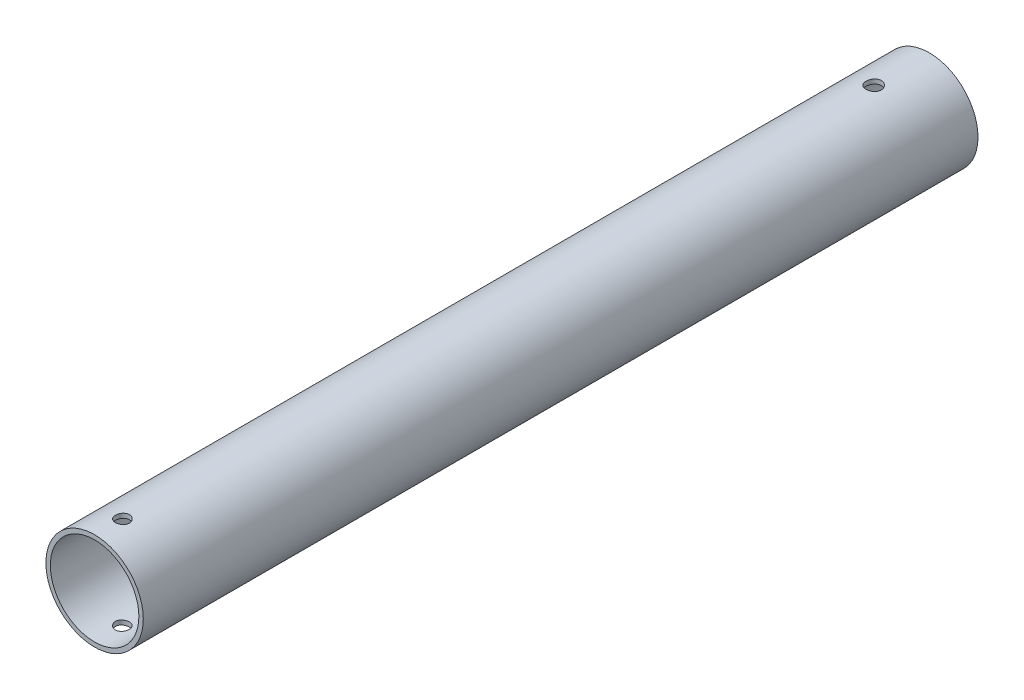
SolidWorks part; units mm, degrees
material "1060 Alloy"
ref_plane "Front Plane" through (0, 0, 0) normal (0, 0, 1) x (1, 0, 0)
ref_plane "Top Plane" through (0, 0, 0) normal (0, 1, 0) x (1, 0, 0)
ref_plane "Right Plane" through (0, 0, 0) normal (1, 0, 0) x (0, 0, -1)
sketch "Sketch1" plane through (0, 0, 0) normal (0, 0, 1) x (1, 0, 0)
  circle A0 centre (0, 0) radius 15.9125
  circle A1 centre (0, 0) radius 17.5
  dimension "D1" = 35
  dimension "D2" = 31.825
extrude "Boss-Extrude1" add sketch "Sketch1" along normal mid plane 300
sketch "Sketch3" plane through (0, 0, 0) normal (0, 1, 0) x (1, 0, 0)
  line L0 (0, 150) -> (0, 130) construction
  line L1 (17.5, 150) -> (-17.5, 150) construction
  dimension "D1" = 20
hole_wizard "M5 Clearance Hole1" positions "Sketch4" profile "Sketch5" hole size "M5" standard "ANSI Metric"
sketch "Sketch4" plane through (0, 0, 0) normal (0, 1, 0) x (1, 0, 0)
  point P0 (0, 130)
sketch "Sketch5" plane through (0, 0, -130) normal (1, 0, 0) x (0, 0, -1)
  line L0 (0, 0) -> (0, 17.5)
  line L1 (0, 17.5) -> (2.75, 17.5)
  line L2 (2.75, 17.5) -> (2.75, 0)
  line L5 (2.75, 0) -> (0, 0)
  line L11 (0, -6.35) -> (0, 107.95) construction
  dimension "Thru Hole Dia." = 5.5
  dimension "Thru Hole Depth" = 17.5
mirror "Mirror1" about plane through (0, 0, 0) normal (0, 1, 0) of "M5 Clearance Hole1"
sketch "Sketch6" plane through (0, 0, 0) normal (0, 1, 0) x (1, 0, 0)
  line L0 (0, -150) -> (0, -140) construction
  line L1 (-17.5, -150) -> (17.5, -150) construction
  circle A0 centre (0, -140) radius 2.5
  circle A1 centre (0, 130) radius 2.5 construction
  dimension "D1" = 10
extrude "Cut-Extrude1" cut sketch "Sketch6" against normal through all both and the other way through all
equation "\"tubeOutDiameter\" = 35mm"
equation "\"wheelShaftDiameter\"= 12mm"
equation "\"wheelThickness\"= 135mm"
equation "\"BearingDiameter\"= 20mm"
equation "\"BearingThickness\"= 10mm"
equation "\"D2@Sketch1\"=\"tubeOutDiameter\"-0.125in"
equation "\"D1@Sketch1\"=\"tubeOutDiameter\""
